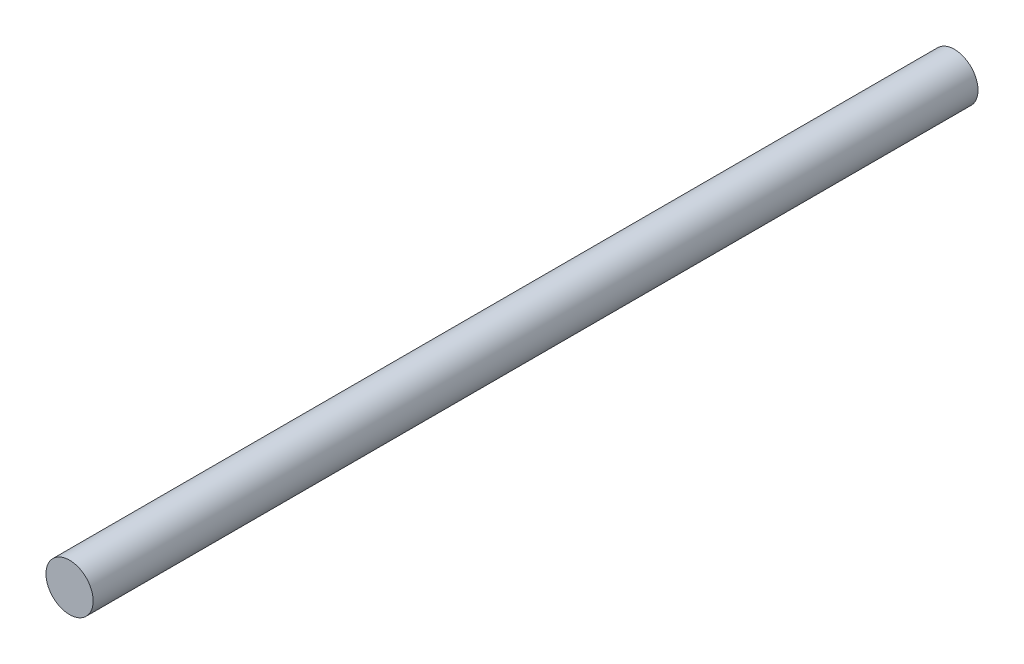
SolidWorks part; units mm, degrees
ref_plane "Front Plane" through (0, 0, 0) normal (0, 0, 1) x (1, 0, 0)
ref_plane "Top Plane" through (0, 0, 0) normal (0, 1, 0) x (1, 0, 0)
ref_plane "Right Plane" through (0, 0, 0) normal (1, 0, 0) x (0, 0, -1)
sketch "Sketch1" plane through (0, 0, 0) normal (0, 0, 1) x (1, 0, 0)
  circle A0 centre (0, 0) radius 4
  dimension "D1" = 8
extrude "Boss-Extrude1" add sketch "Sketch1" along normal blind 150
